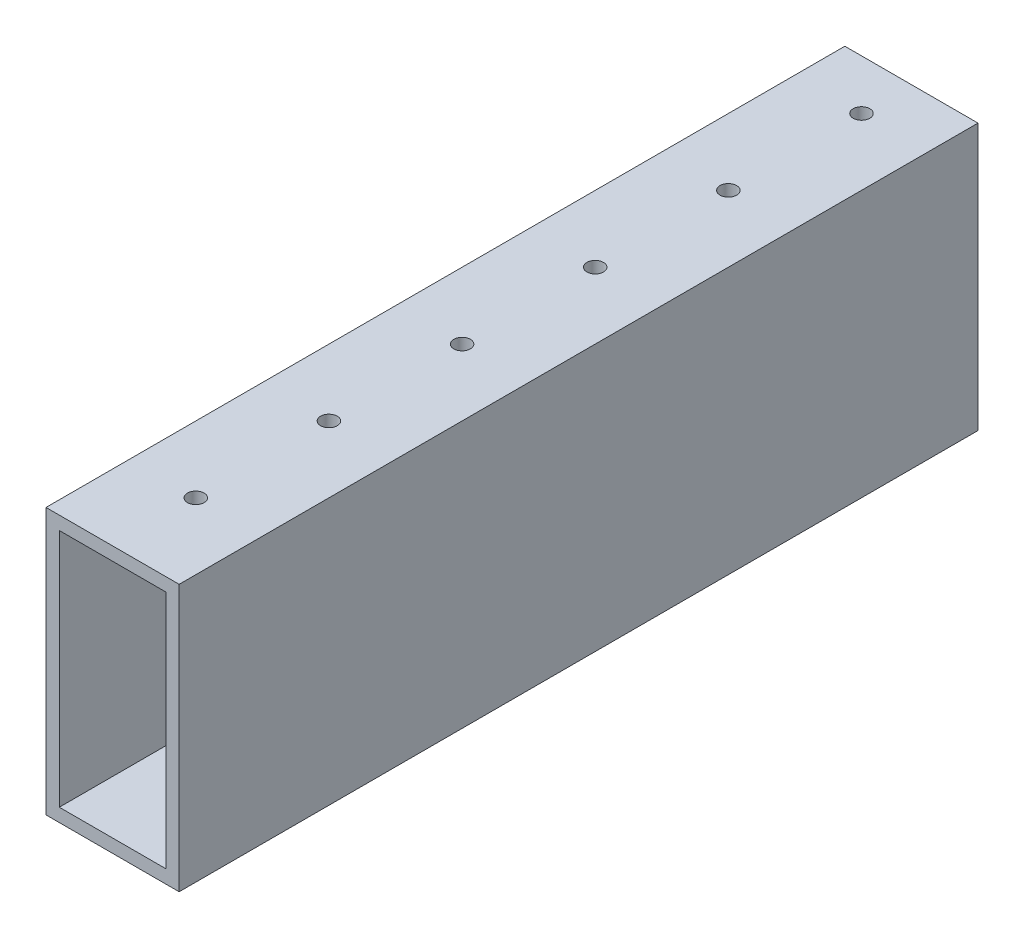
SolidWorks part; units mm, degrees
material "6061-T6 (SS)"
ref_plane "Front Plane" through (0, 0, 0) normal (0, 0, 1) x (1, 0, 0)
ref_plane "Top Plane" through (0, 0, 0) normal (0, 1, 0) x (1, 0, 0)
ref_plane "Right Plane" through (0, 0, 0) normal (1, 0, 0) x (0, 0, -1)
sketch "Sketch1" plane through (0, 0, 0) normal (0, 0, 1) x (1, 0, 0)
  line L1 (0, 0) -> (25.4, 0)
  line L2 (0, 0) -> (0, 50.8)
  line L3 (0, 50.8) -> (25.4, 50.8)
  line L4 (25.4, 0) -> (25.4, 50.8)
  dimension "D1" = 50.8
  dimension "D2" = 25.4
extrude "Extrude-Thin1" add sketch "Sketch1" along normal blind 152.4 thin thin type one direction reverse wall 2.54
sketch "Sketch2" plane through (0, 50.8, 0) normal (0, 1, 0) x (1, 0, 0)
  line L0 (12.7, -152.4) -> (12.7, -664.2692) construction
  line L1 (25.4, -152.4) -> (0, -152.4) construction
  circle A0 centre (12.7, -136.525) radius 1.5875
  dimension "D1" = 15.875
  dimension "D2" = 3.175
extrude "Cut-Extrude1" cut sketch "Sketch2" against normal through all
pattern_linear "LPattern1" count 50 spacing 25.4 along (0, 0, -1) of "Cut-Extrude1"
sketch "Sketch3" [suppressed] plane through (0, 50.8, 0) normal (0, 1, 0) x (1, 0, 0)
  line L0 (25.4, -711.2) -> (25.4, 0) construction
  line L1 (0, -711.2) -> (25.4, -711.2)
  line L2 (0, -711.2) -> (0, -708.025)
  line L3 (0, -708.025) -> (25.4, -708.025)
  line L4 (25.4, -711.2) -> (25.4, -708.025)
  line L6 (0, 0) -> (25.4, 0)
  line L7 (0, 0) -> (0, -3.175)
  line L8 (0, -3.175) -> (25.4, -3.175)
  line L9 (25.4, 0) -> (25.4, -3.175)
  dimension "D1" = 3.175
extrude "Cut-Extrude2" [suppressed] cut sketch "Sketch3" against normal through all
sketch "Sketch5" plane through (0, 50.8, 0) normal (0, 1, 0) x (1, 0, 0)
  line L0 (0, -152.4) -> (0, 0) construction
  line L1 (25.4, 0) -> (0, 0)
  line L2 (25.4, 0) -> (25.4, -3.175)
  line L3 (25.4, -3.175) -> (0, -3.175)
  line L4 (0, 0) -> (0, -3.175)
  dimension "D1" = 3.175
extrude "Cut-Extrude4" [suppressed] cut sketch "Sketch5" against normal through all
sketch "Sketch6" [suppressed] plane through (0, 0, 711.2) normal (0, 0, 1) x (1, 0, 0)
  line L1 (32.8874, 56.0886) -> (-11.3851, 56.0886)
  line L2 (32.8874, 56.0886) -> (32.8874, -11.2785)
  line L3 (32.8874, -11.2785) -> (-11.3851, -11.2785)
  line L4 (-11.3851, 56.0886) -> (-11.3851, -11.2785)
extrude "Cut-Extrude5" [suppressed] cut sketch "Sketch6" against normal blind 6.35
